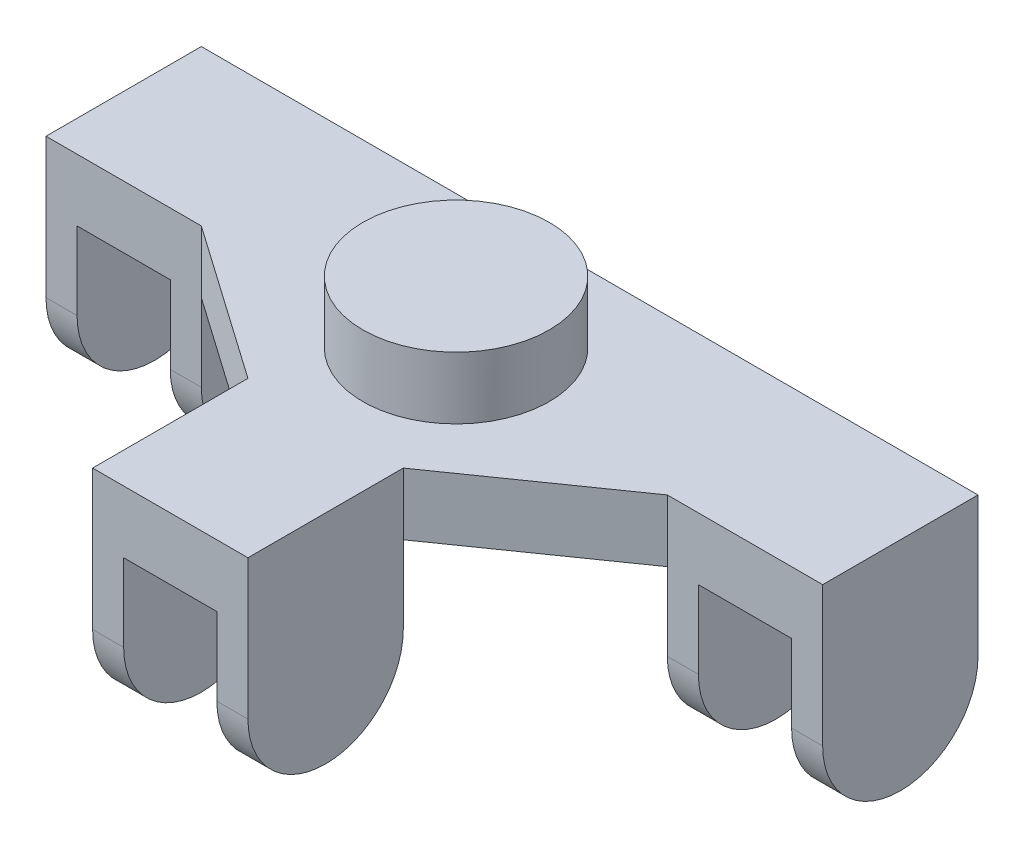
SolidWorks part; units mm, degrees
ref_plane "Front" through (0, 0, 0) normal (0, 0, 1) x (1, 0, 0)
ref_plane "Top" through (0, 0, 0) normal (0, 1, 0) x (1, 0, 0)
ref_plane "Right" through (0, 0, 0) normal (1, 0, 0) x (0, 0, -1)
sketch "草图1" plane through (0, 0, 0) normal (0, 1, 0) x (1, 0, 0)
  line L0 (-31.9558, 0) -> (0, 0) construction
  line L1 (-25, 5) -> (-15, 5)
  line L2 (-25, 5) -> (-25, -5)
  line L3 (-25, -5) -> (-15, -5)
  line L4 (-15, 5) -> (-15, -5)
  line L5 (15, 5) -> (25, 5)
  line L6 (15, 5) -> (15, -5)
  line L7 (15, -5) -> (25, -5)
  line L8 (25, 5) -> (25, -5)
  line L9 (-5, -12) -> (5, -12)
  line L10 (-5, -12) -> (-5, -22)
  line L11 (-5, -22) -> (5, -22)
  line L12 (5, -12) -> (5, -22)
  line L13 (0, 0) -> (0, 15.9462) construction
  dimension "D1" = 10
  dimension "D2" = 10
  dimension "D3" = 10
  dimension "D4" = 10
  dimension "D5" = 5
  dimension "D6" = 5
  dimension "D7" = 10
  dimension "D8" = 10
  dimension "D9" = 5
  dimension "D10" = 15
  dimension "D11" = 15
  dimension "D12" = 12
sketch "草图2" plane through (0, 0, 0) normal (0, 1, 0) x (1, 0, 0)
  line L0 (-25, -5) -> (-25, 23.5912) construction
  line L1 (25, -5) -> (25, 17.5149) construction
  line L2 (-25, 5) -> (25, 5) construction
  line L12 (-5, -22) -> (5, -22)
  line L19 (25, -5) -> (25, 5)
  line L20 (25, 5) -> (-25, 5)
  line L21 (-25, 5) -> (-25, -5)
  line L22 (-25, -5) -> (-15, -5)
  line L23 (-15, -5) -> (-5, -12)
  line L24 (-5, -12) -> (-5, -22)
  line L25 (5, -22) -> (5, -12)
  line L26 (5, -12) -> (15, -5)
  line L27 (15, -5) -> (25, -5)
extrude "凸台-拉伸1" add sketch "草图2" along normal blind 4
extrude "凸台-拉伸2" add sketch "草图1" against normal blind 10
sketch "草图3" plane through (0, 0, -5) normal (0, 0, -1) x (-1, 0, 0)
  line L1 (-25, -10) -> (-15, -10) construction
  line L2 (20, -10) -> (20, 10.9896) construction
  line L3 (15, -10) -> (25, -10) construction
  line L4 (0, -10) -> (0, 9.0404) construction
  line L5 (-5, -10) -> (5, -10) construction
  line L6 (-25, 0) -> (25, 0) construction
  line L7 (-25, 4) -> (-25, -10) construction
  line L8 (25, 4) -> (25, -10) construction
  line L9 (-20, -10) -> (-20, 4.5431) construction
  line L10 (-23, 0) -> (-17, 0)
  line L11 (-23, 0) -> (-23, -12.7458)
  line L12 (-23, -12.7458) -> (-17, -12.7458)
  line L13 (-17, 0) -> (-17, -12.7458)
  line L14 (-3, 0) -> (3, 0)
  line L15 (-3, 0) -> (-3, -12.7458)
  line L16 (-3, -12.7458) -> (3, -12.7458)
  line L17 (3, 0) -> (3, -12.7458)
  line L18 (17, 0) -> (23, 0)
  line L19 (17, 0) -> (17, -13.3873)
  line L20 (17, -13.3873) -> (23, -13.3873)
  line L21 (23, 0) -> (23, -13.3873)
  dimension "D1" = 6
  dimension "D2" = 3
  dimension "D3" = 6
  dimension "D4" = 3
  dimension "D5" = 6
  dimension "D6" = 3
extrude "切除-拉伸1" cut sketch "草图3" against normal through all
sketch "草图4" plane through (25, 0, 0) normal (1, 0, 0) x (0, 0, -1)
  line L2 (-22, -5) -> (-22, -12.806)
  line L3 (-22, -12.806) -> (-12, -12.806)
  line L4 (-12, -5) -> (-12, -12.806)
  line L6 (-5, -5) -> (-5, -13.7387)
  line L7 (-5, -13.7387) -> (5, -13.7387)
  line L8 (5, -5) -> (5, -13.7387)
  arc A0 (-22, -5) -> (-12, -5) centre (-17, -5) ccw
  arc A1 (-5, -5) -> (5, -5) centre (0, -5) ccw
extrude "切除-拉伸2" cut sketch "草图4" against normal through all
sketch "草图5" plane through (0, 4, 0) normal (0, 1, 0) x (1, 0, 0)
  line L0 (0, 5) -> (0, -22) construction
  line L1 (25, 5) -> (-25, 5) construction
  line L2 (-5, -22) -> (5, -22) construction
  circle A0 centre (0, -3.6) radius 6
extrude "凸台-拉伸3" add sketch "草图5" along normal blind 4
